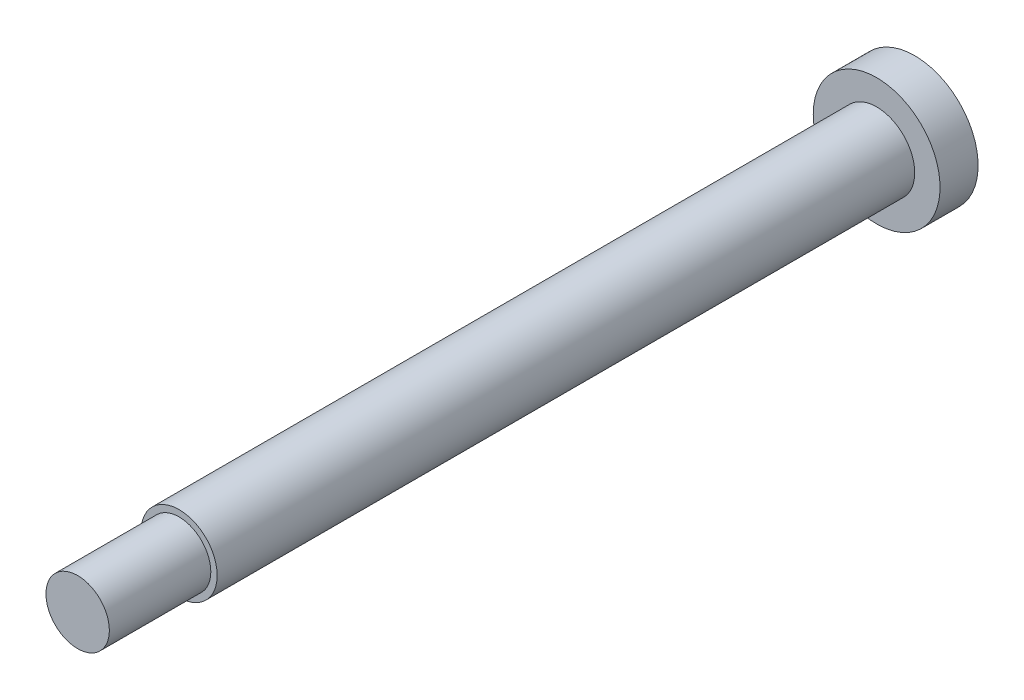
SolidWorks part; units mm, degrees
material "1060 合金"
ref_plane "前视基准面" through (0, 0, 0) normal (0, 0, 1) x (1, 0, 0)
ref_plane "上视基准面" through (0, 0, 0) normal (0, 1, 0) x (1, 0, 0)
ref_plane "右视基准面" through (0, 0, 0) normal (1, 0, 0) x (0, 0, -1)
sketch "草图1" plane through (0, 0, 0) normal (0, 0, 1) x (1, 0, 0)
  circle A0 centre (0, 0) radius 3
  dimension "D1" = 6
extrude "凸台-拉伸1" add sketch "草图1" along normal blind 55
sketch "草图2" plane through (0, 0, 55) normal (0, 0, 1) x (1, 0, 0)
  circle A0 centre (0, 0) radius 2.5
  dimension "D1" = 5
extrude "凸台-拉伸2" add sketch "草图2" along normal blind 8
cosmetic thread "装饰螺纹线1" parameters "D2"=3.242
sketch "草图3" plane through (0, 0, 0) normal (0, 0, -1) x (-1, 0, 0)
  circle A0 centre (0, 0) radius 5
  dimension "D1" = 10
extrude "凸台-拉伸3" add sketch "草图3" along normal blind 3
